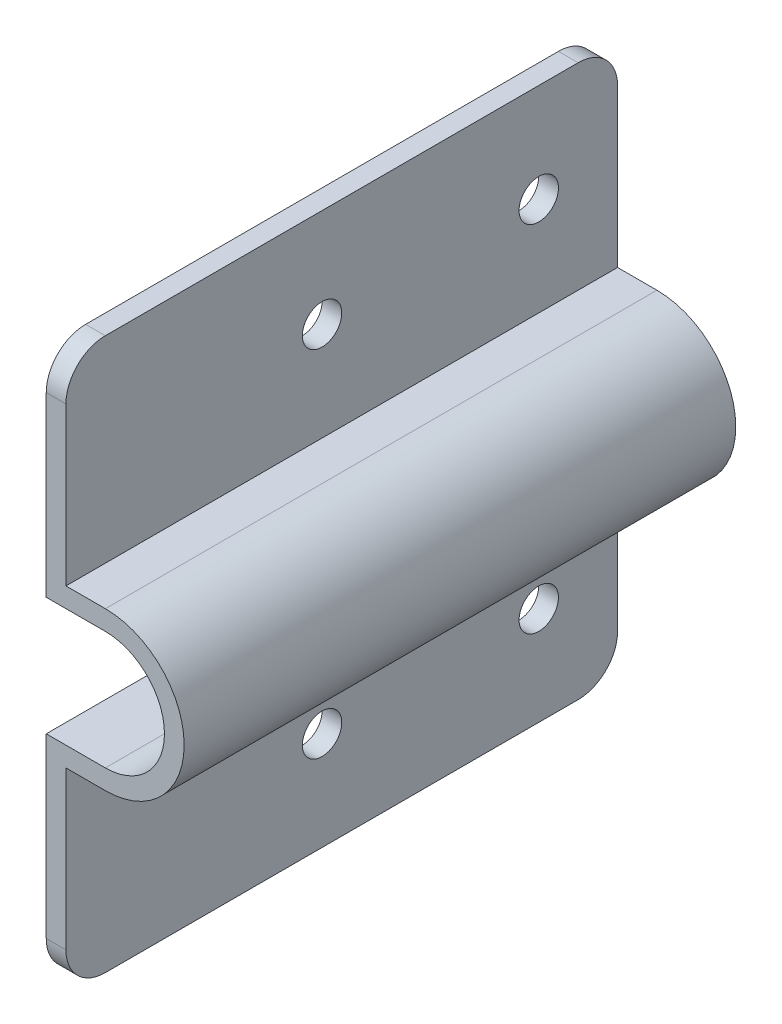
SolidWorks part; units mm, degrees
material "6061-T6 (SS)"
ref_plane "Front Plane" through (0, 0, 0) normal (0, 0, 1) x (1, 0, 0)
ref_plane "Top Plane" through (0, 0, 0) normal (0, 1, 0) x (1, 0, 0)
ref_plane "Right Plane" through (0, 0, 0) normal (1, 0, 0) x (0, 0, -1)
sketch "Sketch1" plane through (0, 0, 0) normal (0, 0, 1) x (1, 0, 0)
  line L0 (10.16, 323.0894) -> (10.16, 234.1894)
  line L1 (10.16, -19.9824) -> (10.16, 1018.8869) construction
  line L2 (10.16, 278.6394) -> (19.685, 278.6394) construction
  line L3 (10.16, 234.1894) -> (13.335, 234.1894)
  line L4 (10.16, 234.1894) -> (10.16, 323.0894)
  line L5 (10.16, 323.0894) -> (13.335, 323.0894)
  line L6 (13.335, 234.1894) -> (13.335, 323.0894)
  line L7 (19.685, 288.1644) -> (13.335, 288.1644)
  line L8 (19.685, 269.1144) -> (13.335, 269.1144)
  line L9 (19.685, 291.3394) -> (13.335, 291.3394)
  line L10 (19.685, 265.9394) -> (13.335, 265.9394)
  line L11 (13.335, 288.1644) -> (10.16, 288.1644)
  line L12 (13.335, 269.1144) -> (10.16, 269.1144)
  circle A0 centre (19.685, 278.6394) radius 9.525
  circle A1 centre (19.685, 278.6394) radius 12.7
  ellipse E0 centre (16.7619, 278.6394) end of major axis (26.2869, 278.6394) minor radius 9.5021 construction
  dimension "D4" = 19.05
  dimension "D5" = 3.175
  dimension "D1" = 88.9
  dimension "D2" = 44.45
  dimension "D3" = 3.175
extrude "Boss-Extrude1" add sketch "Sketch1" against normal blind 88.9 contours L11 L6 L5 L0 | A1 L9 L6 L7 | A1 L7 A0 L8 | A1 L8 L6 L10 | L6 L12 L0 L3 | L6 A1 L11 | L12 A1 L6
sketch "Sketch2" plane through (13.335, 0, 0) normal (1, 0, 0) x (0, 0, -1)
  line L0 (88.9, 307.2144) -> (0, 307.2144) construction
  line L1 (88.9, 291.3394) -> (88.9, 323.0894) construction
  line L2 (0, 291.3394) -> (0, 323.0894) construction
  line L3 (0, 250.0644) -> (88.9, 250.0644) construction
  line L4 (0, 234.1894) -> (0, 265.9394) construction
  line L5 (88.9, 234.1894) -> (88.9, 265.9394) construction
  circle A0 centre (41.275, 250.0644) radius 3.175
  circle A1 centre (76.2, 250.0644) radius 3.175
  circle A2 centre (76.2, 307.2144) radius 3.175
  circle A3 centre (41.275, 307.2144) radius 3.175
  dimension "D1" = 6.35
  dimension "D2" = 12.7
  dimension "D3" = 12.7
  dimension "D4" = 34.925
  dimension "D5" = 34.925
extrude "Cut-Extrude1" cut sketch "Sketch2" against normal through all
fillet "Fillet1" radius 6.35 4 edges at (11.7475, 234.1894, 0) (11.7475, 234.1894, -88.9) (11.7475, 323.0894, 0) (11.7475, 323.0894, -88.9)
